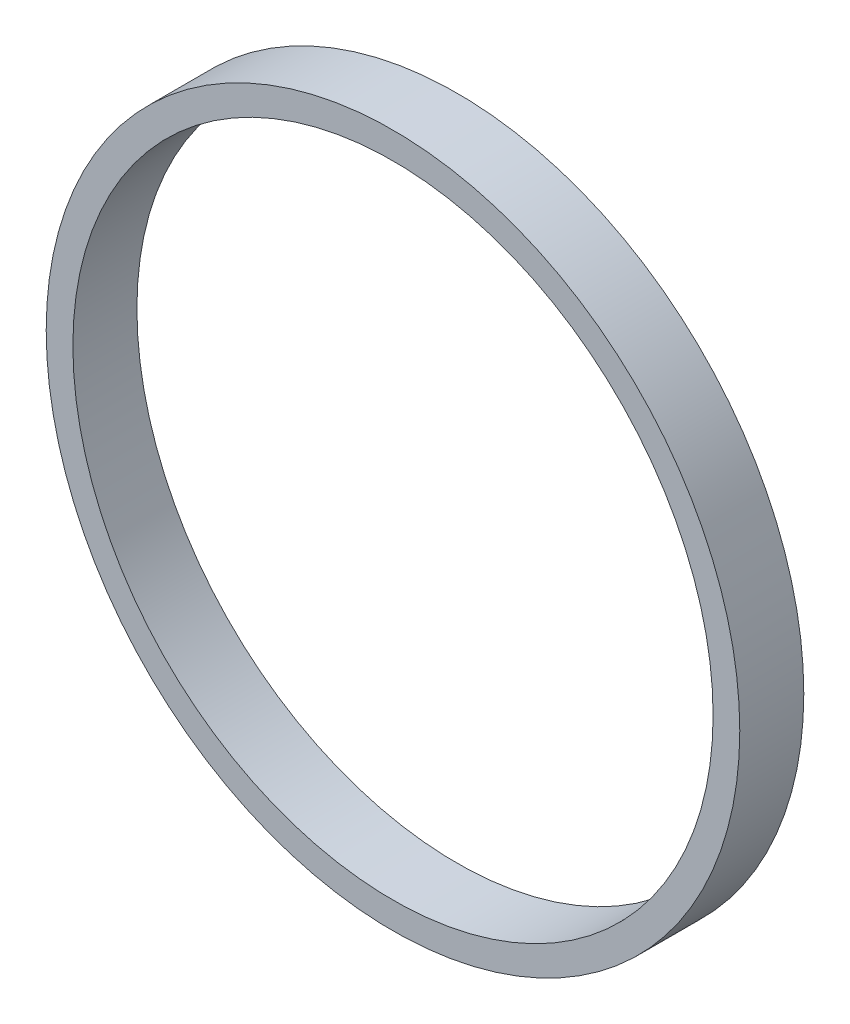
SolidWorks part; units mm, degrees
ref_plane "Front Plane" through (0, 0, 0) normal (0, 0, 1) x (1, 0, 0)
ref_plane "Top Plane" through (0, 0, 0) normal (0, 1, 0) x (1, 0, 0)
ref_plane "Right Plane" through (0, 0, 0) normal (1, 0, 0) x (0, 0, -1)
sketch "Sketch1" plane through (0, 0, 0) normal (0, 0, 1) x (1, 0, 0)
  circle A0 centre (0, 0) radius 30
  circle A1 centre (0, 0) radius 32.5
  dimension "D1" = 60
  dimension "D2" = 65
extrude "Boss-Extrude1" add sketch "Sketch1" along normal blind 6
